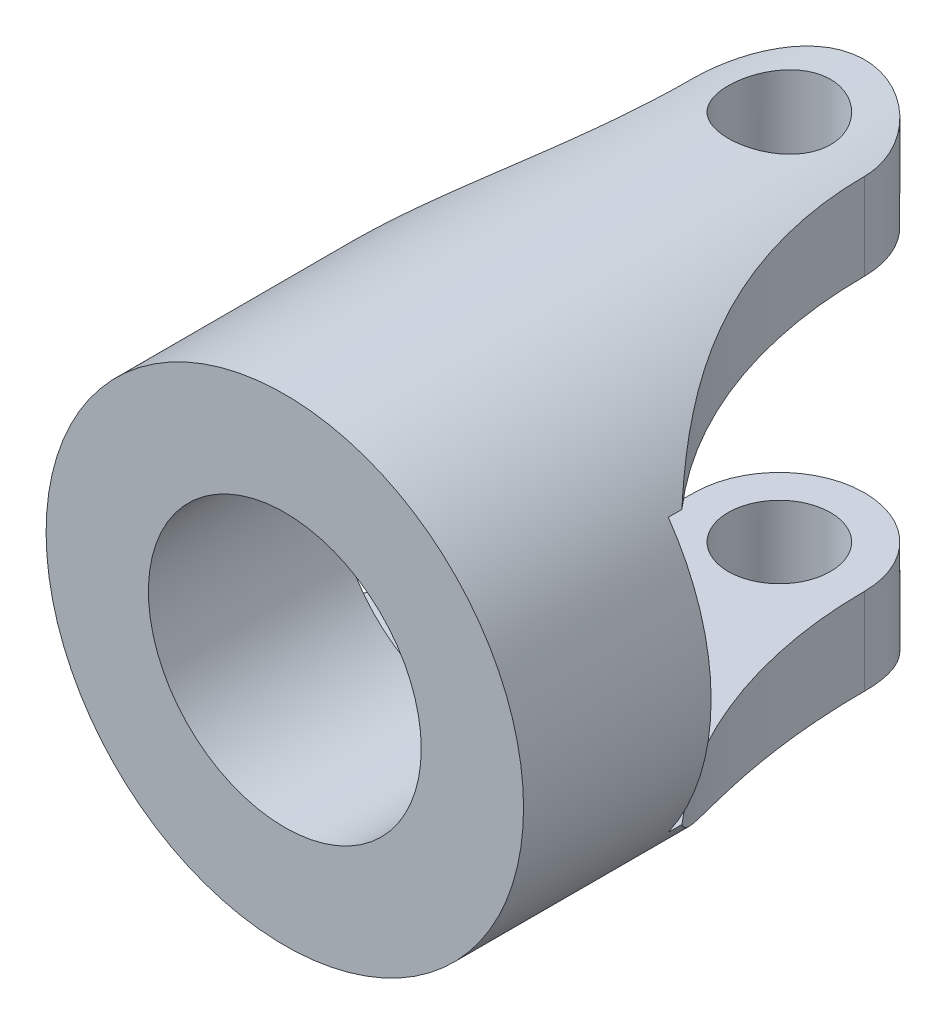
SolidWorks part; units mm, degrees
ref_plane "Front Plane" through (0, 0, 0) normal (0, 0, 1) x (1, 0, 0)
ref_plane "Top Plane" through (0, 0, 0) normal (0, 1, 0) x (1, 0, 0)
ref_plane "Right Plane" through (0, 0, 0) normal (1, 0, 0) x (0, 0, -1)
sketch "Sketch1" plane through (0, 0, 0) normal (0, 0, 1) x (1, 0, 0)
  circle A0 centre (0, 0) radius 4
  circle A1 centre (0, 0) radius 7
  dimension "D1" = 8
  dimension "D2" = 14
extrude "Boss-Extrude1" add sketch "Sketch1" along normal blind 17
sketch "Sketch2" plane through (0, 0, 0) normal (0, 1, 0) x (1, 0, 0)
  line L0 (0, 0) -> (0, -17) construction
  line L1 (-7, -17) -> (7, -17) construction
  line L2 (-7, -11.5) -> (7, -11.5) construction
  line L3 (-7, 0) -> (-7, -17) construction
  line L4 (7, -17) -> (7, 0) construction
  line L5 (-7, -11.5) -> (-7, 0)
  line L6 (-7, 0) -> (0, 1)
  line L7 (0, 1) -> (7, 0)
  line L8 (7, 0) -> (-7, 0) construction
  line L9 (7, 0) -> (7, -11.5)
  line L10 (-7, -11.5) -> (-6.1094, -11.5)
  line L11 (6.1094, -11.5) -> (7, -11.5)
  circle A0 centre (0, -2.5) radius 1.5
  arc A1 (2.5, -2.5) -> (-2.5, -2.5) centre (0, -2.5) ccw
  arc A4 (-6.1094, -11.5) -> (-2.5, -2.5) centre (-15.5253, -2.5) ccw
  arc A5 (6.1094, -11.5) -> (2.5, -2.5) centre (15.5253, -2.5) cw
  dimension "D2" = 3
  dimension "D3" = 2.5
  dimension "D1" = 5.5
  dimension "D5" = 1
  dimension "D6" = 0.8906
extrude "Cut-Extrude1" cut sketch "Sketch2" against normal through all both and the other way through all contours A0 | L9 L11 A5 A1 A4 L10 L5 L6 L7
sketch "Sketch3" plane through (0, 0, 0) normal (1, 0, 0) x (0, 0, -1)
  line L0 (-11.5, 7) -> (-11.5, -7) construction
  line L1 (-4, 7) -> (-17, 7) construction
  line L2 (-17, -7) -> (-4, -7) construction
  line L3 (-17, 7) -> (-17, -7) construction
  line L4 (0, 4) -> (-11.5, 4)
  line L5 (0, -4) -> (-11.5, -4)
  line L6 (-11.5, -4) -> (-11.5, 4)
  line L8 (0, 4) -> (0, -4)
  spline S0 degree 2 poles (0, 4) (-1.404, 3.1225) (-2.5, 3.1225) knots 0 0 0 0.3245 0.3245 0.3245 weights 0.0015 0.002311 0.003122 construction
  dimension "D1" = 5.5
extrude "Cut-Extrude2" cut sketch "Sketch3" against normal through all both and the other way through all
sketch "Sketch8" plane through (0, 0, 0) normal (0, 1, 0) x (1, 0, 0)
  line L0 (0, -2.5) -> (0, -17) construction
  line L1 (-7, -17) -> (7, -17) construction
